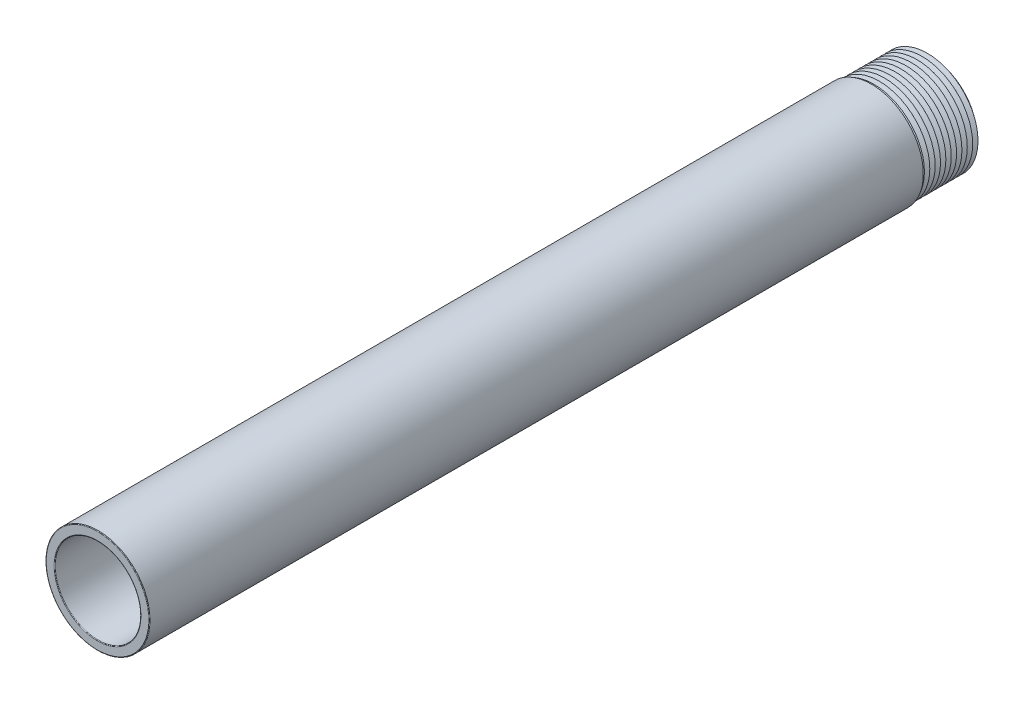
SolidWorks part; units mm, degrees
material "6061 Alloy"
ref_plane "Front Plane" through (0, 0, 0) normal (0, 0, 1) x (1, 0, 0)
ref_plane "Top Plane" through (0, 0, 0) normal (0, 1, 0) x (1, 0, 0)
ref_plane "Right Plane" through (0, 0, 0) normal (1, 0, 0) x (0, 0, -1)
sketch "Sketch1" plane through (0, 0, 0) normal (0, 0, 1) x (1, 0, 0)
  circle A0 centre (0, 0) radius 11.0744
  circle A1 centre (0, 0) radius 9.144
extrude "Extrude1" add sketch "Sketch1" along normal blind 177.8
ref_plane "Plane1" through (-11.0744, 0, 0) normal (1, 0, 0) x (0, 0, -1)
sketch "Sketch6" plane through (-11.0744, 0, 0) normal (1, 0, 0) x (0, 0, -1)
  line L0 (-88.9, -1.2192) -> (-63.5, -1.2192)
  line L1 (-50.8, 1.2192) -> (-25.4, 1.2192)
  line L2 (-50.8, -1.2192) -> (-25.4, -1.2192)
  line L3 (-88.9, 1.2192) -> (-63.5, 1.2192)
  line L4 (-127, -1.2192) -> (-101.6, -1.2192)
  line L5 (-127, 1.2192) -> (-101.6, 1.2192)
  line L6 (-165.1, -1.2192) -> (-139.7, -1.2192)
  line L7 (-165.1, 1.2192) -> (-139.7, 1.2192)
  arc A0 (-63.5, 1.2192) -> (-63.5, -1.2192) centre (-63.5, 0) cw
  arc A1 (-88.9, 1.2192) -> (-88.9, -1.2192) centre (-88.9, 0) ccw
  arc A2 (-50.8, 1.2192) -> (-50.8, -1.2192) centre (-50.8, 0) ccw
  arc A3 (-25.4, 1.2192) -> (-25.4, -1.2192) centre (-25.4, 0) cw
  arc A4 (-101.6, 1.2192) -> (-101.6, -1.2192) centre (-101.6, 0) cw
  arc A5 (-127, 1.2192) -> (-127, -1.2192) centre (-127, 0) ccw
  arc A6 (-139.7, 1.2192) -> (-139.7, -1.2192) centre (-139.7, 0) cw
  arc A7 (-165.1, 1.2192) -> (-165.1, -1.2192) centre (-165.1, 0) ccw
extrude "Cut-Extrude1" cut sketch "Sketch6" along normal blind 2.54
sketch "Sketch9" plane through (0, 0, 0) normal (1, 0, 0) x (0, 0, -1)
  line L3 (-12.7, 9.906) -> (-12.1867, 10.795)
  line L4 (-12.1867, 10.795) -> (-11.6735, 9.906)
  line L5 (-11.6735, 9.906) -> (-11.557, 9.906)
  line L6 (-11.0437, 10.795) -> (-10.5305, 9.906)
  line L7 (-11.557, 9.906) -> (-11.0437, 10.795)
  line L8 (-9.9007, 10.795) -> (-9.3875, 9.906)
  line L9 (-10.414, 9.906) -> (-9.9007, 10.795)
  line L10 (-8.7577, 10.795) -> (-8.2445, 9.906)
  line L11 (-9.271, 9.906) -> (-8.7577, 10.795)
  line L12 (-7.6147, 10.795) -> (-7.1015, 9.906)
  line L13 (-8.128, 9.906) -> (-7.6147, 10.795)
  line L14 (-6.4717, 10.795) -> (-5.9585, 9.906)
  line L15 (-6.985, 9.906) -> (-6.4717, 10.795)
  line L16 (-5.3287, 10.795) -> (-4.8155, 9.906)
  line L17 (-5.842, 9.906) -> (-5.3287, 10.795)
  line L18 (-4.1857, 10.795) -> (-3.6725, 9.906)
  line L19 (-4.699, 9.906) -> (-4.1857, 10.795)
  line L20 (-3.0427, 10.795) -> (-2.5295, 9.906)
  line L21 (-3.556, 9.906) -> (-3.0427, 10.795)
  line L22 (-1.8997, 10.795) -> (-1.3865, 9.906)
  line L23 (-2.413, 9.906) -> (-1.8997, 10.795)
  line L24 (-0.7567, 10.795) -> (-0.2435, 9.906)
  line L25 (-1.27, 9.906) -> (-0.7567, 10.795)
  line L26 (-10.5305, 9.906) -> (-10.414, 9.906)
  line L27 (-9.3875, 9.906) -> (-9.271, 9.906)
  line L28 (-8.2445, 9.906) -> (-8.128, 9.906)
  line L29 (-7.1015, 9.906) -> (-6.985, 9.906)
  line L30 (-5.9585, 9.906) -> (-5.842, 9.906)
  line L31 (-4.8155, 9.906) -> (-4.699, 9.906)
  line L32 (-3.6725, 9.906) -> (-3.556, 9.906)
  line L33 (-2.5295, 9.906) -> (-2.413, 9.906)
  line L34 (-1.3865, 9.906) -> (-1.27, 9.906)
  line L35 (-0.2435, 9.906) -> (0, 9.906)
  line L36 (0, 9.906) -> (0, 11.3664)
  line L37 (0, 11.3664) -> (-12.7, 11.3664)
  line L38 (-12.7, 11.3664) -> (-12.7, 9.906)
revolve "Cut-Revolve1" cut sketch "Sketch9" angle 360 about axis through (0, 0, 177.8) along (0, 0, -1)
fillet "Fillet1" radius 0.127 36 edges at (-9.1429, 0.1386, 49.5887) (-9.0624, -1.2192, 38.1) (-9.1429, 0.1386, 24.1887) (-11.0736, 0.1353, 49.5883) (-11.0071, -1.2192, 38.1) (-11.0736, 0.1353, 24.1883) (-9.1429, 0.1386, 163.8887) (-9.0624, -1.2192, 152.4) (-9.1429, 0.1386, 138.4887) (-11.0736, 0.1353, 163.8883) (-11.0071, -1.2192, 152.4) (-11.0736, 0.1353, 138.4883) (-9.1429, 0.1386, 125.7887) (-9.0624, -1.2192, 114.3) (-9.1429, 0.1386, 100.3887) (-11.0736, 0.1353, 125.7883) (-11.0071, -1.2192, 114.3) (-11.0736, 0.1353, 100.3883) (-9.1429, 0.1386, 87.6887) (-9.0624, -1.2192, 76.2) (-9.1429, 0.1386, 62.2887) (-11.0736, 0.1353, 87.6883) (-11.0071, -1.2192, 76.2) (-11.0736, 0.1353, 62.2883) (9.144, 0, 0) (9.144, 0, 177.8) (11.0744, 0, 177.8) (-9.0624, 1.2192, 38.1) (-11.0071, 1.2192, 38.1) (-9.0624, 1.2192, 152.4) (-11.0071, 1.2192, 152.4) (-9.0624, 1.2192, 114.3) (-11.0071, 1.2192, 114.3) (-9.0624, 1.2192, 76.2) (-11.0071, 1.2192, 76.2) (9.906, 0, 0)
